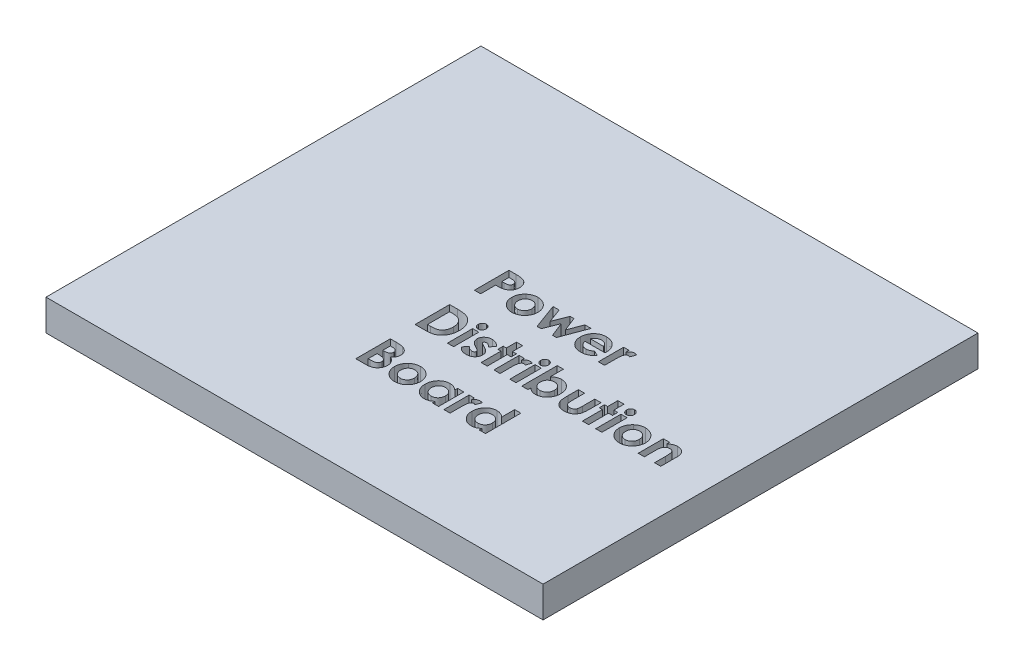
SolidWorks part; units mm, degrees
ref_plane "Front Plane" through (0, 0, 0) normal (0, 0, 1) x (1, 0, 0)
ref_plane "Top Plane" through (0, 0, 0) normal (0, 1, 0) x (1, 0, 0)
ref_plane "Right Plane" through (0, 0, 0) normal (1, 0, 0) x (0, 0, -1)
sketch "Sketch1" plane through (0, 0, 0) normal (0, 1, 0) x (1, 0, 0)
  line L1 (0, 0) -> (160, 0)
  line L2 (0, 0) -> (0, 140)
  line L3 (0, 140) -> (160, 140)
  line L4 (160, 0) -> (160, 140)
  dimension "D1" = 160
  dimension "D2" = 140
extrude "Boss-Extrude1" add sketch "Sketch1" along normal blind 10
sketch "Sketch2" plane through (0, 10, 0) normal (0, 1, 0) x (1, 0, 0)
  line L0 (65.7475, 70.8786) -> (139.1576, 70.8786) construction
  text T0 "<b>Power</b>\r\n<b>Distribution</b>\r\n<b>Board</b>" font "Century Gothic" height in points 42
extrude "Cut-Extrude1" cut sketch "Sketch2" against normal blind 10
